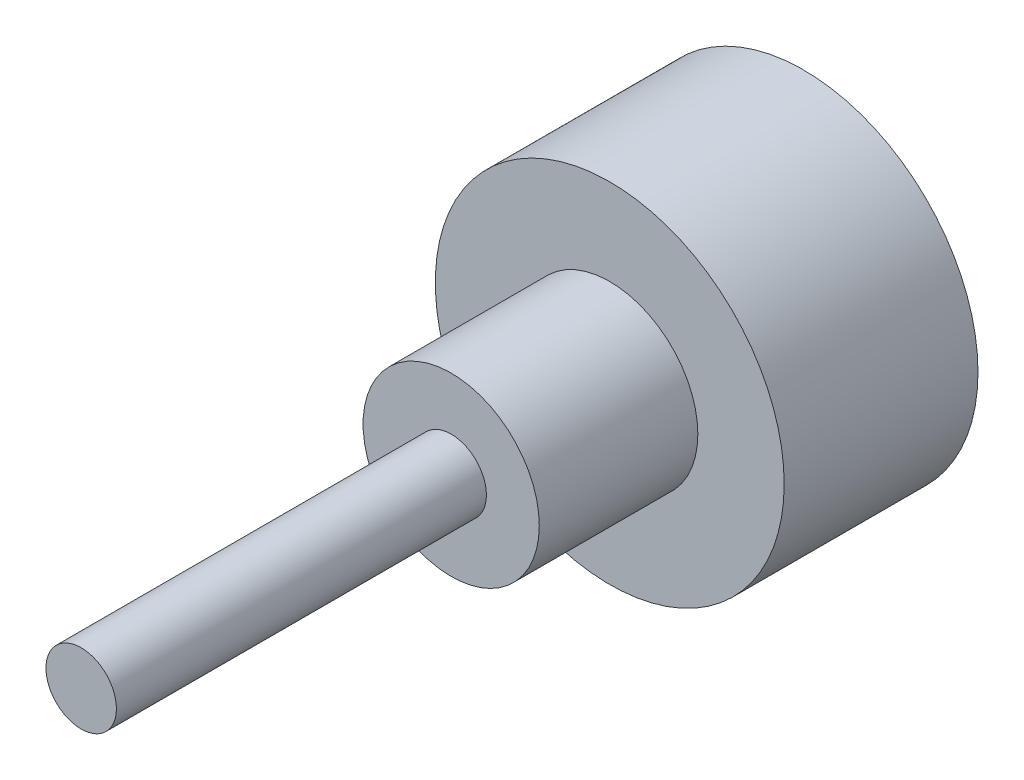
SolidWorks part; units mm, degrees
ref_plane "Alzado" through (0, 0, 0) normal (0, 0, 1) x (1, 0, 0)
ref_plane "Planta" through (0, 0, 0) normal (0, 1, 0) x (1, 0, 0)
ref_plane "Vista lateral" through (0, 0, 0) normal (1, 0, 0) x (0, 0, -1)
sketch "Croquis1" plane through (0, 0, 0) normal (0, 0, 1) x (1, 0, 0)
  circle A0 centre (0, 0) radius 7.9
  circle A1 centre (0, 0) radius 9.9
  dimension "D1" = 15.8
  dimension "D2" = 2
extrude "Saliente-Extruir1" add sketch "Croquis1" along normal blind 10
sketch "Croquis2" plane through (0, 0, 10) normal (0, 0, 1) x (1, 0, 0)
  circle A0 centre (0, 0) radius 9.9
  circle A1 centre (0, 0) radius 9.9 construction
extrude "Saliente-Extruir2" add sketch "Croquis2" along normal blind 1
sketch "Croquis4" plane through (0, 0, 11) normal (0, 0, 1) x (1, 0, 0)
  circle A0 centre (0, 0) radius 5
  dimension "D1" = 10
extrude "Saliente-Extruir4" add sketch "Croquis4" along normal blind 9
sketch "Croquis3" plane through (0, 0, 11) normal (0, 0, 1) x (1, 0, 0)
  circle A0 centre (0, 0) radius 2
  dimension "D1" = 4
extrude "Saliente-Extruir3" add sketch "Croquis3" along normal blind 30
